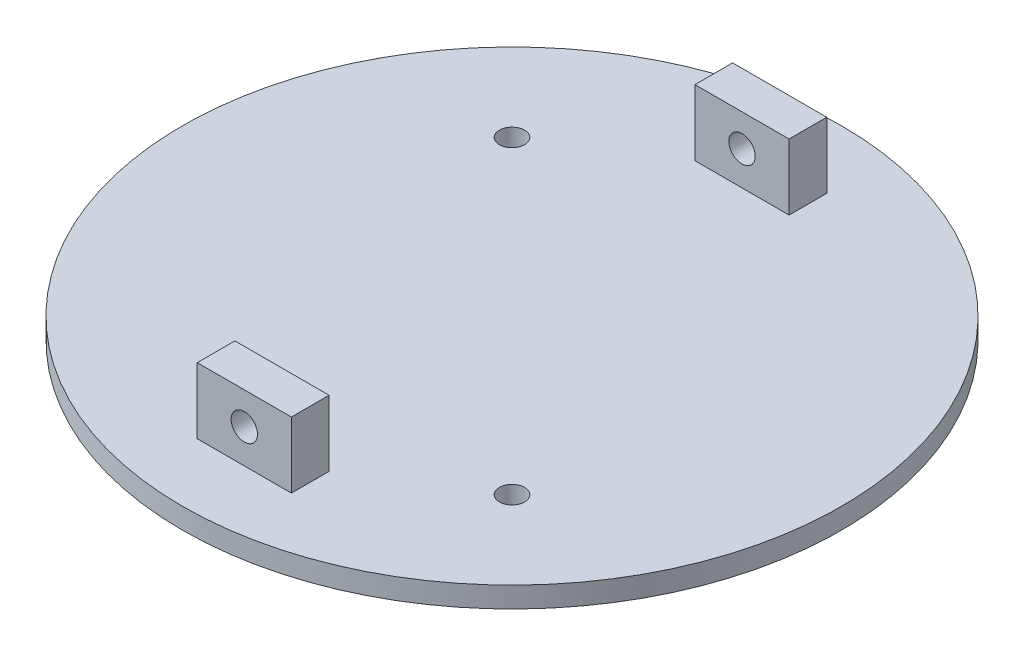
SolidWorks part; units mm, degrees
ref_plane "Front Plane" through (0, 0, 0) normal (0, 0, 1) x (1, 0, 0)
ref_plane "Top Plane" through (0, 0, 0) normal (0, 1, 0) x (1, 0, 0)
ref_plane "Right Plane" through (0, 0, 0) normal (1, 0, 0) x (0, 0, -1)
sketch "Sketch1" plane through (0, 0, 0) normal (0, 1, 0) x (1, 0, 0)
  line L1 (0, 0) -> (88.9, 0) construction
  line L2 (0, 0) -> (0, 88.9) construction
  line L3 (0, 88.9) -> (88.9, 88.9) construction
  line L4 (88.9, 0) -> (88.9, 88.9) construction
  circle A0 centre (65.314, 23.586) radius 1.7 construction
  circle A1 centre (23.586, 65.314) radius 1.7 construction
  circle A2 centre (65.314, 23.586) radius 1.7
  circle A3 centre (23.586, 65.314) radius 1.7
  circle A5 centre (44.45, 44.45) radius 44.45
  point P12 (44.45, 44.45)
  dimension "D2" = 44.45
  dimension "D1" = 88.9
  dimension "D3" = 44.45
extrude "Boss-Extrude1" add sketch "Sketch1" along normal blind 2.794
sketch "Sketch3" plane through (0, 2.794, 0) normal (0, 1, 0) x (1, 0, 0)
  line L5 (50.256, 13.97) -> (50.256, 8.89) construction
  line L6 (50.256, 13.97) -> (37.556, 13.97) construction
  line L7 (37.556, 13.97) -> (37.556, 8.89) construction
  line L8 (50.256, 8.89) -> (37.556, 8.89) construction
  line L13 (38.644, 74.93) -> (38.644, 80.01) construction
  line L14 (38.644, 74.93) -> (51.344, 74.93) construction
  line L15 (51.344, 74.93) -> (51.344, 80.01) construction
  line L16 (38.644, 80.01) -> (51.344, 80.01) construction
  line L21 (38.644, 80.01) -> (51.344, 80.01)
  line L22 (38.644, 80.01) -> (38.644, 74.93)
  line L23 (38.644, 74.93) -> (51.344, 74.93)
  line L24 (51.344, 80.01) -> (51.344, 74.93)
  line L25 (37.556, 13.97) -> (50.256, 13.97)
  line L26 (37.556, 13.97) -> (37.556, 8.89)
  line L27 (37.556, 8.89) -> (50.256, 8.89)
  line L28 (50.256, 13.97) -> (50.256, 8.89)
  circle A0 centre (44.45, 44.45) radius 44.45 construction
  circle A1 centre (44.45, 44.45) radius 44.45 construction
  circle A2 centre (44.45, 44.45) radius 41.275 construction
  point P27 (44.45, 44.45)
  dimension "D1" = 82.55
extrude "Boss-Extrude2" add sketch "Sketch3" along normal blind 8.89
sketch "Sketch4" plane through (0, 0, -8.89) normal (0, 0, 1) x (1, 0, 0)
  line L0 (37.556, 2.794) -> (50.256, 2.794) construction
  circle A0 centre (43.906, 7.366) radius 1.778
  dimension "D1" = 3.556
  dimension "D2" = 4.572
extrude "Cut-Extrude1" cut sketch "Sketch4" against normal blind 13.208
pattern_circular "CirPattern1" count 2 over 360 about axis through (44.45, 7.366, 0) along (0, 0, 1) of "Cut-Extrude1"
